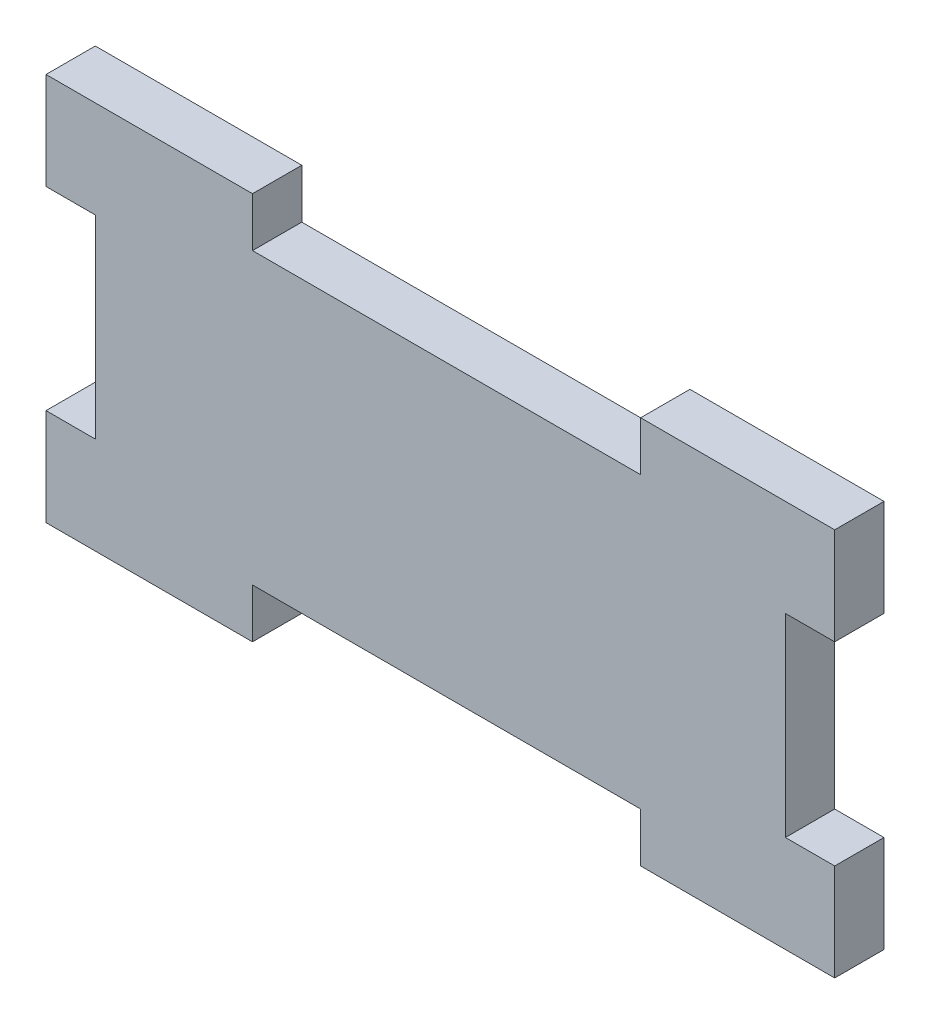
SolidWorks part; units mm, degrees
ref_plane "Front Plane" through (0, 0, 0) normal (0, 0, 1) x (1, 0, 0)
ref_plane "Top Plane" through (0, 0, 0) normal (0, 1, 0) x (1, 0, 0)
ref_plane "Right Plane" through (0, 0, 0) normal (1, 0, 0) x (0, 0, -1)
sketch "Sketch1" plane through (0, 0, 0) normal (0, 0, 1) x (1, 0, 0)
  line L1 (0, 0) -> (101.6, 0)
  line L2 (0, 0) -> (0, 50)
  line L3 (0, 50) -> (101.6, 50)
  line L4 (101.6, 0) -> (101.6, 50)
  dimension "D1" = 50
  dimension "D2" = 101.6
extrude "Boss-Extrude1" add sketch "Sketch1" along normal blind 6.35
sketch "Sketch3" plane through (0, 0, 6.35) normal (0, 0, 1) x (1, 0, 0)
  line L0 (0, 50) -> (0, 0) construction
  line L1 (0, 37.5) -> (6.35, 37.5)
  line L2 (0, 37.5) -> (0, 12.5)
  line L3 (0, 12.5) -> (6.35, 12.5)
  line L4 (6.35, 37.5) -> (6.35, 12.5)
  line L5 (0, 12.5) -> (0, 0) construction
  dimension "D1" = 6.35
  dimension "D2" = 25
  dimension "D3" = 12.5
extrude "Cut-Extrude2" cut sketch "Sketch3" against normal through all
sketch "Sketch4" plane through (0, 0, 6.35) normal (0, 0, 1) x (1, 0, 0)
  line L0 (101.6, 0) -> (101.6, 50) construction
  line L1 (101.6, 37.5) -> (95.25, 37.5)
  line L2 (101.6, 37.5) -> (101.6, 12.5)
  line L3 (101.6, 12.5) -> (95.25, 12.5)
  line L4 (95.25, 37.5) -> (95.25, 12.5)
  line L5 (101.6, 12.5) -> (101.6, 0) construction
  line L6 (101.6, 50) -> (0, 50) construction
  line L7 (26.6, 50) -> (76.6, 50)
  line L8 (26.6, 50) -> (26.6, 43.65)
  line L9 (26.6, 43.65) -> (76.6, 43.65)
  line L10 (76.6, 50) -> (76.6, 43.65)
  line L11 (0, 50) -> (26.6, 50) construction
  line L12 (0, 0) -> (101.6, 0) construction
  line L13 (26.6, 0) -> (76.6, 0)
  line L14 (26.6, 0) -> (26.6, 6.35)
  line L15 (26.6, 6.35) -> (76.6, 6.35)
  line L16 (76.6, 0) -> (76.6, 6.35)
  dimension "D1" = 25
  dimension "D2" = 6.35
  dimension "D3" = 12.5
  dimension "D4" = 50
  dimension "D5" = 26.6
  dimension "6.35mm" = 6.35
  dimension "D7" = 6.35
  dimension "D8" = 50
extrude "Cut-Extrude3" cut sketch "Sketch4" against normal through all
